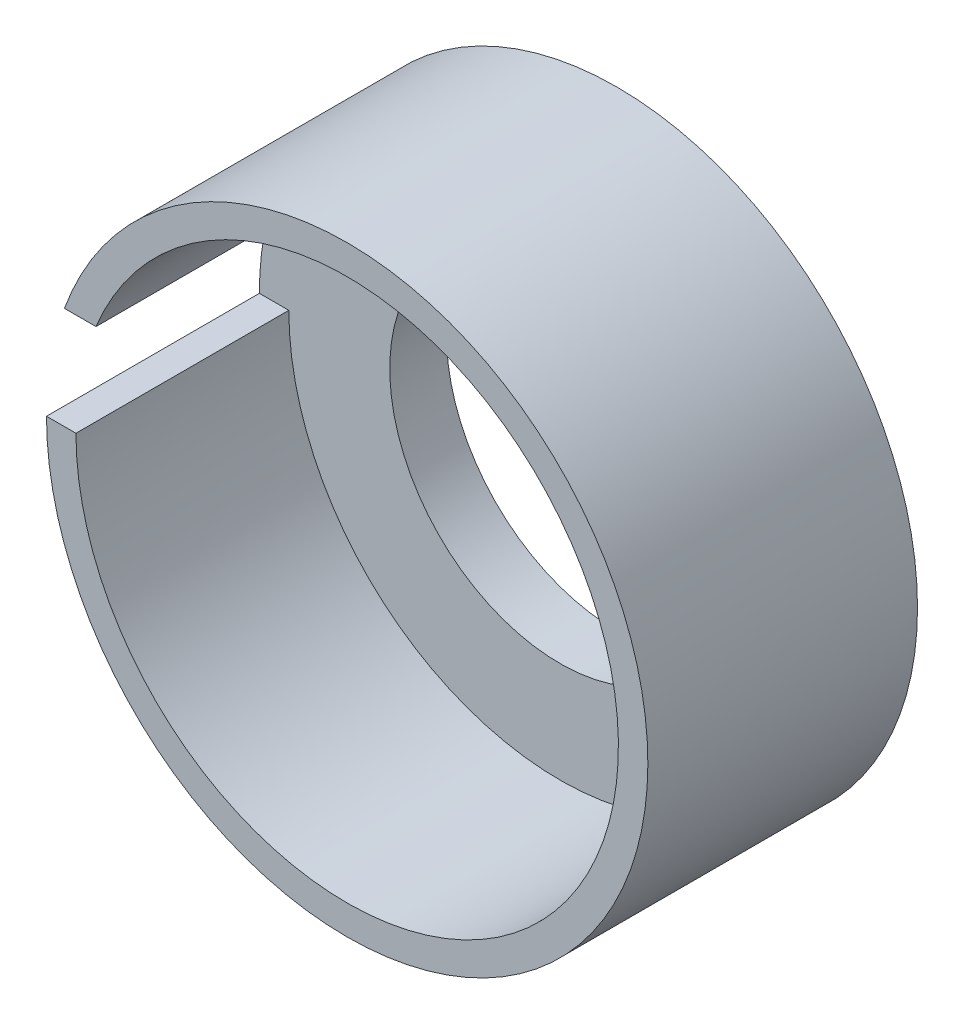
SolidWorks part; units mm, degrees
ref_plane "Front Plane" through (0, 0, 0) normal (0, 0, 1) x (1, 0, 0)
ref_plane "Top Plane" through (0, 0, 0) normal (0, 1, 0) x (1, 0, 0)
ref_plane "Right Plane" through (0, 0, 0) normal (1, 0, 0) x (0, 0, -1)
sketch "Sketch1" plane through (0, 0, 0) normal (0, 0, 1) x (1, 0, 0)
  circle A0 centre (0, 0) radius 38.125
  circle A1 centre (0, 0) radius 42.375
  dimension "D1" = 76.25
  dimension "D2" = 84.75
extrude "Boss-Extrude1" add sketch "Sketch1" along normal blind 8 contours A1
sketch "Sketch2" plane through (0, 0, 8) normal (0, 0, 1) x (1, 0, 0)
  line L0 (-38.225, 0) -> (-42.375, 0)
  line L1 (-35.3978, 14.4273) -> (-39.8434, 14.4273)
  circle A0 centre (0, 0) radius 38.225
  circle A1 centre (0, 0) radius 42.375 construction
  circle A2 centre (0, 0) radius 42.375
  circle M1 centre (0, 0) radius 42.375
  dimension "D1" = 76.45
  dimension "D2" = 360
extrude "Boss-Extrude2" add sketch "Sketch2" along normal blind 30 contours A0 L0 L1 M1
sketch "Sketch3" plane through (0, 0, 8) normal (0, 0, 1) x (1, 0, 0)
  line L2 (-35.3978, 14.4273) -> (-39.8434, 14.4273)
  line L3 (-42.375, 0) -> (-38.225, 0)
  line L4 (-35.3978, 14.4273) -> (-39.8434, 14.4273)
  line L5 (-42.375, 0) -> (-38.225, 0)
  arc A0 (-38.225, 0) -> (-35.3978, 14.4273) centre (0, 0) ccw construction
  arc A1 (-42.375, 0) -> (-39.8434, 14.4273) centre (0, 0) ccw construction
  arc A2 (-38.225, 0) -> (-35.3978, 14.4273) centre (0, 0) ccw
  arc A3 (-42.375, 0) -> (-39.8434, 14.4273) centre (0, 0) ccw
  circle A4 centre (0, 0) radius 38.225
  arc A6 (-38.225, 0) -> (-35.3978, 14.4273) centre (0, 0) ccw
  arc A7 (-39.8434, 14.4273) -> (-42.375, 0) centre (0, 0) ccw
  arc A8 (-38.225, 0) -> (-35.3978, 14.4273) centre (0, 0) ccw
  arc A9 (-39.8434, 14.4273) -> (-42.375, 0) centre (0, 0) ccw
  line M6 (-35.3978, 14.4273) -> (-39.8434, 14.4273)
  arc M7 (-39.8434, 14.4273) -> (-42.375, 0) centre (0, 0) ccw
  line M8 (-42.375, 0) -> (-38.225, 0)
  dimension "D1" = 0
extrude "Boss-Extrude3" [suppressed] add sketch "Sketch3" along normal blind 6 contours A4 M6 M7 M8
sketch "Sketch4" plane through (0, 0, 8) normal (0, 0, 1) x (1, 0, 0)
  circle A0 centre (0, 0) radius 24
  dimension "D1" = 48
extrude "Cut-Extrude1" cut sketch "Sketch4" against normal blind 20
